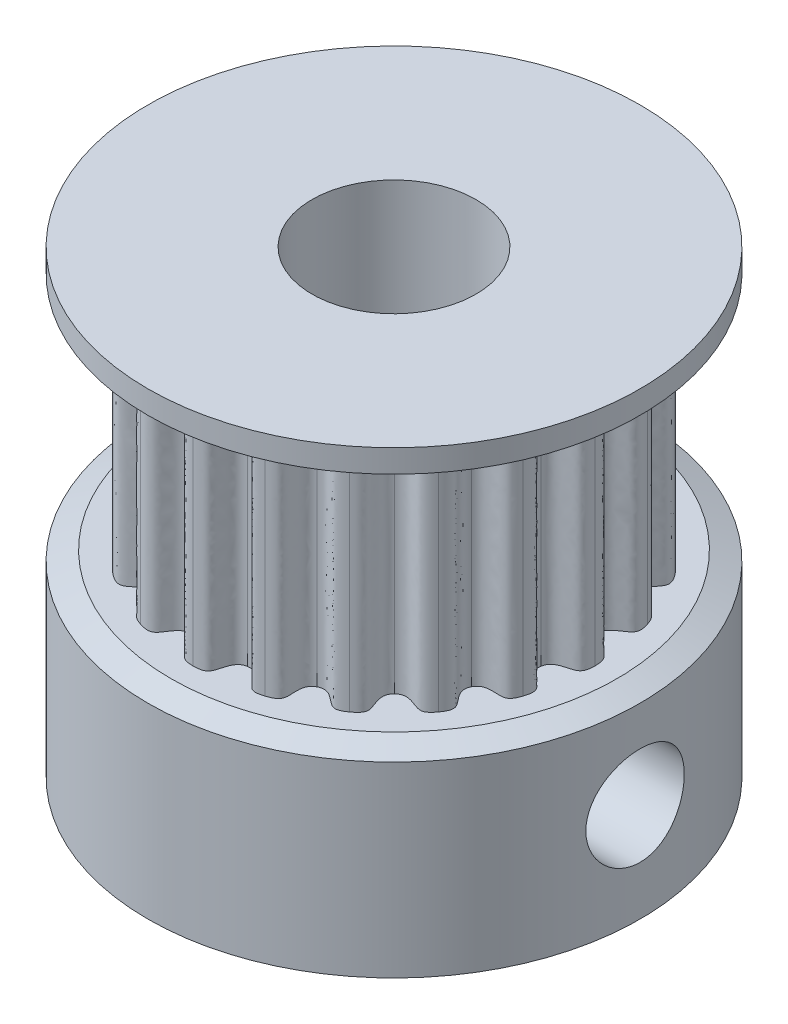
SolidWorks part; units mm, degrees
material "6063-T5"
ref_plane "Front Plane" through (0, 0, 0) normal (0, 0, 1) x (1, 0, 0)
ref_plane "Top Plane" through (0, 0, 0) normal (0, 1, 0) x (1, 0, 0)
ref_plane "Right Plane" through (0, 0, 0) normal (1, 0, 0) x (0, 0, -1)
sketch "Sketch1" plane through (0, 0, 0) normal (0, 1, 0) x (1, 0, 0)
  circle A0 centre (0, 0) radius 7.5
  dimension "D1" = 15
extrude "Boss-Extrude1" add sketch "Sketch1" along normal blind 6 contours A0
sketch "Sketch2" plane through (0, 6, 0) normal (0, 1, 0) x (1, 0, 0)
  line L0 (0, 6.1275) -> (0, 5.3775) construction
  line L1 (1.8935, 5.8276) -> (1.6617, 5.1143) construction
  line L2 (0.9585, 6.052) -> (0.8412, 5.3113) construction
  circle A0 centre (0, 0) radius 6.1275
  circle A1 centre (0, 0) radius 5.3775 construction
  spline S0 degree 3 poles (0, 6.1275) (0.3458, 6.1275) (0.4361, 5.9343) (0.5475, 5.3578) (0.8412, 5.3113) knots 0 0 0 0 0.372907 1 1 1 1
  spline S1 degree 3 poles (1.8935, 5.8276) (1.5646, 5.9344) (1.419, 5.7786) (1.135, 5.2647) (0.8412, 5.3113) knots 0 0 0 0 0.372907 1 1 1 1
  spline S2 degree 3 poles (3.6016, 4.9572) (3.3681, 5.1259) (3.0728, 5.1167) (2.729, 4.6418) (2.4347, 4.7947) knots 0 0 0 0 0.382401 1 1 1 1
  spline S3 degree 3 poles (1.8935, 5.8276) (2.162, 5.7403) (2.3095, 5.4903) (2.1415, 4.9436) (2.4347, 4.7947) knots 0 0 0 0 0.37474 1 1 1 1
  spline S4 degree 3 poles (4.9572, 3.6016) (4.7873, 3.8342) (4.5035, 3.9167) (4.0298, 3.5713) (3.7972, 3.8077) knots 0 0 0 0 0.382401 1 1 1 1
  spline S5 degree 3 poles (3.6016, 4.9572) (3.83, 4.7913) (3.8931, 4.5079) (3.5643, 4.0399) (3.7972, 3.8077) knots 0 0 0 0 0.37474 1 1 1 1
  spline S6 degree 3 poles (5.8276, 1.8935) (5.7378, 2.1672) (5.4934, 2.3334) (4.9362, 2.1512) (4.788, 2.4479) knots 0 0 0 0 0.382401 1 1 1 1
  spline S7 degree 3 poles (4.9572, 3.6016) (5.1231, 3.3733) (5.0955, 3.0843) (4.6383, 2.7408) (4.788, 2.4479) knots 0 0 0 0 0.37474 1 1 1 1
  spline S8 degree 3 poles (6.1275, 0) (6.1267, 0.288) (5.9456, 0.5216) (5.3594, 0.5206) (5.3101, 0.8485) knots 0 0 0 0 0.382401 1 1 1 1
  spline S9 degree 3 poles (5.8276, 1.8935) (5.9148, 1.625) (5.7992, 1.3587) (5.2582, 1.1733) (5.3101, 0.8485) knots 0 0 0 0 0.37474 1 1 1 1
  spline S10 degree 3 poles (5.8276, -1.8935) (5.9158, -1.6193) (5.8158, -1.3412) (5.2579, -1.1611) (5.3124, -0.8339) knots 0 0 0 0 0.382401 1 1 1 1
  spline S11 degree 3 poles (6.1275, 0) (6.1275, -0.2823) (5.9353, -0.4999) (5.3634, -0.509) (5.3124, -0.8339) knots 0 0 0 0 0.37474 1 1 1 1
  spline S12 degree 3 poles (4.9572, -3.6016) (5.1259, -3.3681) (5.1167, -3.0728) (4.6418, -2.729) (4.7947, -2.4347) knots 0 0 0 0 0.382401 1 1 1 1
  spline S13 degree 3 poles (5.8276, -1.8935) (5.7403, -2.162) (5.4903, -2.3095) (4.9436, -2.1415) (4.7947, -2.4347) knots 0 0 0 0 0.37474 1 1 1 1
  spline S14 degree 3 poles (3.6016, -4.9572) (3.8342, -4.7873) (3.9167, -4.5035) (3.5713, -4.0298) (3.8077, -3.7972) knots 0 0 0 0 0.382401 1 1 1 1
  spline S15 degree 3 poles (4.9572, -3.6016) (4.7913, -3.83) (4.5079, -3.8931) (4.0399, -3.5643) (3.8077, -3.7972) knots 0 0 0 0 0.37474 1 1 1 1
  spline S16 degree 3 poles (1.8935, -5.8276) (2.1672, -5.7378) (2.3334, -5.4934) (2.1512, -4.9362) (2.4479, -4.788) knots 0 0 0 0 0.382401 1 1 1 1
  spline S17 degree 3 poles (3.6016, -4.9572) (3.3733, -5.1231) (3.0843, -5.0955) (2.7408, -4.6383) (2.4479, -4.788) knots 0 0 0 0 0.37474 1 1 1 1
  spline S18 degree 3 poles (0, -6.1275) (0.288, -6.1267) (0.5216, -5.9456) (0.5206, -5.3594) (0.8485, -5.3101) knots 0 0 0 0 0.382401 1 1 1 1
  spline S19 degree 3 poles (1.8935, -5.8276) (1.625, -5.9148) (1.3587, -5.7992) (1.1733, -5.2582) (0.8485, -5.3101) knots 0 0 0 0 0.37474 1 1 1 1
  spline S20 degree 3 poles (-1.8935, -5.8276) (-1.6193, -5.9158) (-1.3412, -5.8158) (-1.1611, -5.2579) (-0.8339, -5.3124) knots 0 0 0 0 0.382401 1 1 1 1
  spline S21 degree 3 poles (0, -6.1275) (-0.2823, -6.1275) (-0.4999, -5.9353) (-0.509, -5.3634) (-0.8339, -5.3124) knots 0 0 0 0 0.37474 1 1 1 1
  spline S22 degree 3 poles (-3.6016, -4.9572) (-3.3681, -5.1259) (-3.0728, -5.1167) (-2.729, -4.6418) (-2.4347, -4.7947) knots 0 0 0 0 0.382401 1 1 1 1
  spline S23 degree 3 poles (-1.8935, -5.8276) (-2.162, -5.7403) (-2.3095, -5.4903) (-2.1415, -4.9436) (-2.4347, -4.7947) knots 0 0 0 0 0.37474 1 1 1 1
  spline S24 degree 3 poles (-4.9572, -3.6016) (-4.7873, -3.8342) (-4.5035, -3.9167) (-4.0298, -3.5713) (-3.7972, -3.8077) knots 0 0 0 0 0.382401 1 1 1 1
  spline S25 degree 3 poles (-3.6016, -4.9572) (-3.83, -4.7913) (-3.8931, -4.5079) (-3.5643, -4.0399) (-3.7972, -3.8077) knots 0 0 0 0 0.37474 1 1 1 1
  spline S26 degree 3 poles (-5.8276, -1.8935) (-5.7378, -2.1672) (-5.4934, -2.3334) (-4.9362, -2.1512) (-4.788, -2.4479) knots 0 0 0 0 0.382401 1 1 1 1
  spline S27 degree 3 poles (-4.9572, -3.6016) (-5.1231, -3.3733) (-5.0955, -3.0843) (-4.6383, -2.7408) (-4.788, -2.4479) knots 0 0 0 0 0.37474 1 1 1 1
  spline S28 degree 3 poles (-6.1275, 0) (-6.1267, -0.288) (-5.9456, -0.5216) (-5.3594, -0.5206) (-5.3101, -0.8485) knots 0 0 0 0 0.382401 1 1 1 1
  spline S29 degree 3 poles (-5.8276, -1.8935) (-5.9148, -1.625) (-5.7992, -1.3587) (-5.2582, -1.1733) (-5.3101, -0.8485) knots 0 0 0 0 0.37474 1 1 1 1
  spline S30 degree 3 poles (-5.8276, 1.8935) (-5.9158, 1.6193) (-5.8158, 1.3412) (-5.2579, 1.1611) (-5.3124, 0.8339) knots 0 0 0 0 0.382401 1 1 1 1
  spline S31 degree 3 poles (-6.1275, 0) (-6.1275, 0.2823) (-5.9353, 0.4999) (-5.3634, 0.509) (-5.3124, 0.8339) knots 0 0 0 0 0.37474 1 1 1 1
  spline S32 degree 3 poles (-4.9572, 3.6016) (-5.1259, 3.3681) (-5.1167, 3.0728) (-4.6418, 2.729) (-4.7947, 2.4347) knots 0 0 0 0 0.382401 1 1 1 1
  spline S33 degree 3 poles (-5.8276, 1.8935) (-5.7403, 2.162) (-5.4903, 2.3095) (-4.9436, 2.1415) (-4.7947, 2.4347) knots 0 0 0 0 0.37474 1 1 1 1
  spline S34 degree 3 poles (-3.6016, 4.9572) (-3.8342, 4.7873) (-3.9167, 4.5035) (-3.5713, 4.0298) (-3.8077, 3.7972) knots 0 0 0 0 0.382401 1 1 1 1
  spline S35 degree 3 poles (-4.9572, 3.6016) (-4.7913, 3.83) (-4.5079, 3.8931) (-4.0399, 3.5643) (-3.8077, 3.7972) knots 0 0 0 0 0.37474 1 1 1 1
  spline S36 degree 3 poles (-1.8935, 5.8276) (-2.1672, 5.7378) (-2.3334, 5.4934) (-2.1512, 4.9362) (-2.4479, 4.788) knots 0 0 0 0 0.382401 1 1 1 1
  spline S37 degree 3 poles (-3.6016, 4.9572) (-3.3733, 5.1231) (-3.0843, 5.0955) (-2.7408, 4.6383) (-2.4479, 4.788) knots 0 0 0 0 0.37474 1 1 1 1
  spline S38 degree 3 poles (0, 6.1275) (-0.288, 6.1267) (-0.5216, 5.9456) (-0.5206, 5.3594) (-0.8485, 5.3101) knots 0 0 0 0 0.382401 1 1 1 1
  spline S39 degree 3 poles (-1.8935, 5.8276) (-1.625, 5.9148) (-1.3587, 5.7992) (-1.1733, 5.2582) (-0.8485, 5.3101) knots 0 0 0 0 0.37474 1 1 1 1
  point P10 (0, 0)
  point P14 (0, 0)
  point P153 (0, 0)
  dimension "D1" = 12.2549
  dimension "D2" = 0.75
  dimension "D3" = 2
  dimension "D4" = 2
extrude "Boss-Extrude2" add sketch "Sketch2" along normal blind 7 contours S39 S36 S37 S34 S35 S32 S33 S30 S31 S28 S29 S26 S27 S24 S25 S22 S23 S20 S21 S18 S19 S16 S17 S14 S15 S12 S13 S10 S11 S8 S9 S6 S7 S4 S5 S2 S3 S1 S0 S38
sketch "Sketch3" plane through (0, 13, 0) normal (0, 1, 0) x (1, 0, 0)
  circle A0 centre (0, 0) radius 7.5 construction
  circle A1 centre (0, 0) radius 7.5
extrude "Boss-Extrude3" add sketch "Sketch3" along normal blind 1
chamfer "Chamfer1" distance 0.7 distance2 0.3 1 edges at (0, 13, 7.5)
chamfer "Chamfer2" distance 0.3 distance2 0.7 1 edges at (0, 6, 7.5)
sketch "Sketch4" plane through (0, 0, 0) normal (0, -1, 0) x (1, 0, 0)
  circle A0 centre (0, 0) radius 2.5
  dimension "D1" = 5
extrude "Cut-Extrude1" cut sketch "Sketch4" against normal through all
sketch "Sketch5" plane through (0, 0, 0) normal (1, 0, 0) x (0, 0, -1)
  circle A0 centre (0, 3) radius 1.5
  dimension "D1" = 3
  dimension "D2" = 3
extrude "Cut-Extrude2" cut sketch "Sketch5" along normal through all
sketch "Sketch6" plane through (0, 0, 0) normal (0, 0, 1) x (1, 0, 0)
  circle A0 centre (0, 3) radius 1.5
  dimension "D1" = 3
  dimension "D2" = 3
extrude "Cut-Extrude3" cut sketch "Sketch6" against normal through all
ref_plane "Plane1" through (0, 9.5, 0) normal (0, 1, 0) x (1, 0, 0)
sketch "Sketch7" plane through (0, 6, 0) normal (0, 1, 0) x (1, 0, 0)
  circle A0 centre (0, 0) radius 6.1275 construction
